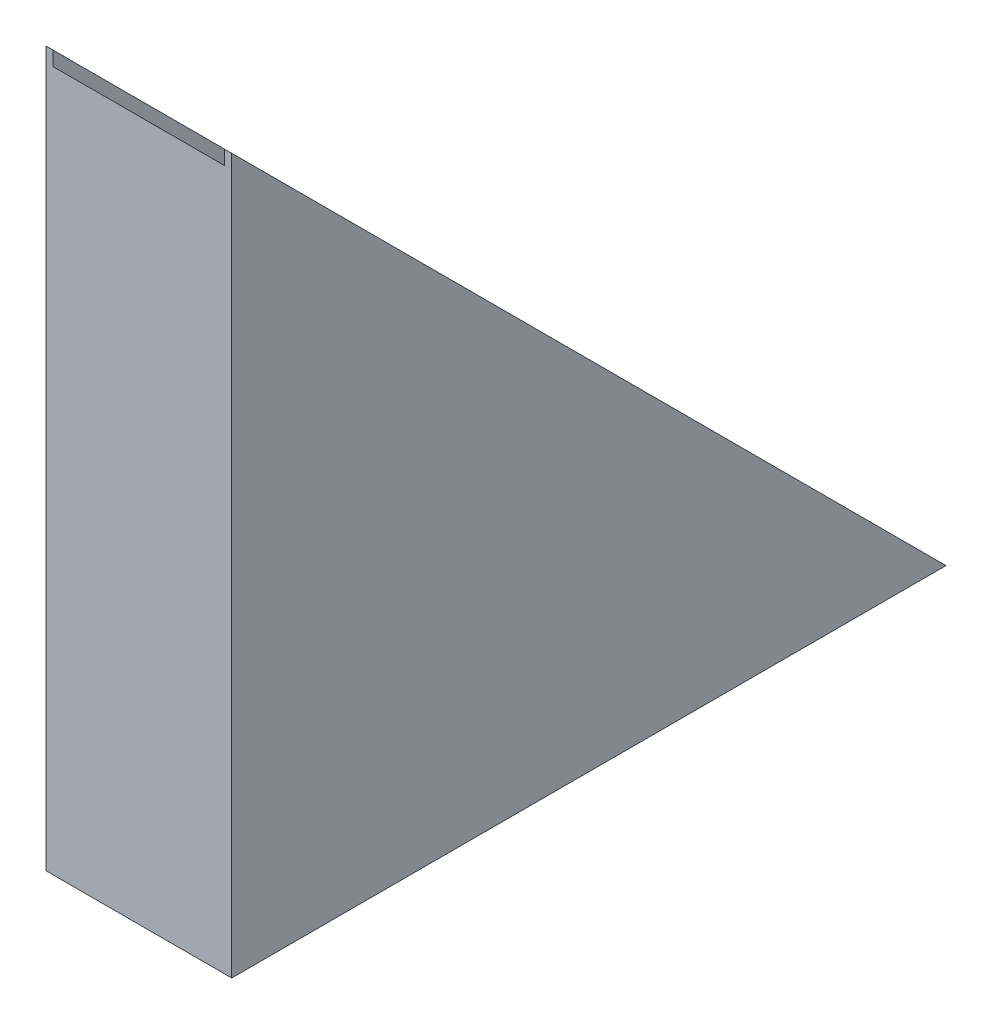
SolidWorks part; units mm, degrees
ref_plane "Front Plane" through (0, 0, 0) normal (0, 0, 1) x (1, 0, 0)
ref_plane "Top Plane" through (0, 0, 0) normal (0, 1, 0) x (1, 0, 0)
ref_plane "Right Plane" through (0, 0, 0) normal (1, 0, 0) x (0, 0, -1)
sketch "Sketch1" plane through (0, 0, 0) normal (1, 0, 0) x (0, 0, -1)
  line L0 (0, 0) -> (2500, 0)
  line L1 (2500, 0) -> (0, 2500)
  line L2 (0, 2500) -> (0, 0)
  dimension "D1" = 45
  dimension "D2" = 2500
extrude "Boss-Extrude1" add sketch "Sketch1" along normal blind 650
sketch "Sketch2" plane through (0, 0, 0) normal (0, 0, 1) x (1, 0, 0)
  line L0 (650, 2500) -> (0, 2500) construction
  line L1 (25, 2500) -> (625, 2500)
  line L2 (25, 2500) -> (25, 2450)
  line L3 (25, 2450) -> (625, 2450)
  line L4 (625, 2500) -> (625, 2450)
  line L5 (0, 2500) -> (0, 0) construction
  dimension "D1" = 600
  dimension "D2" = 50
  dimension "D3" = 25
sweep "Cut-Sweep1" cut profiles "Sketch2" path edge at (0, 1250, -1250)
